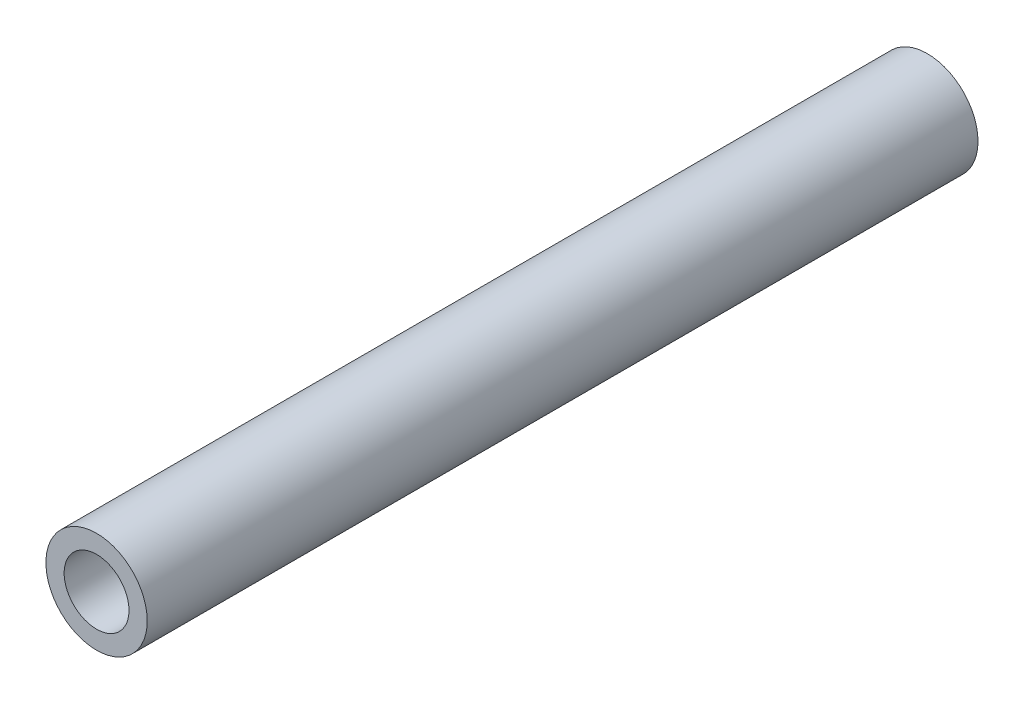
SolidWorks part; units mm, degrees
ref_plane "Front" through (0, 0, 0) normal (0, 0, 1) x (1, 0, 0)
ref_plane "Top" through (0, 0, 0) normal (0, 1, 0) x (1, 0, 0)
ref_plane "Right" through (0, 0, 0) normal (1, 0, 0) x (0, 0, -1)
sketch "Sketch1" plane through (0, 0, 0) normal (0, 0, 1) x (1, 0, 0)
  circle A0 centre (0, 0) radius 2.5
  circle A1 centre (0, 0) radius 1.6
extrude "Boss-Extrude1" add sketch "Sketch1" along normal blind 41
